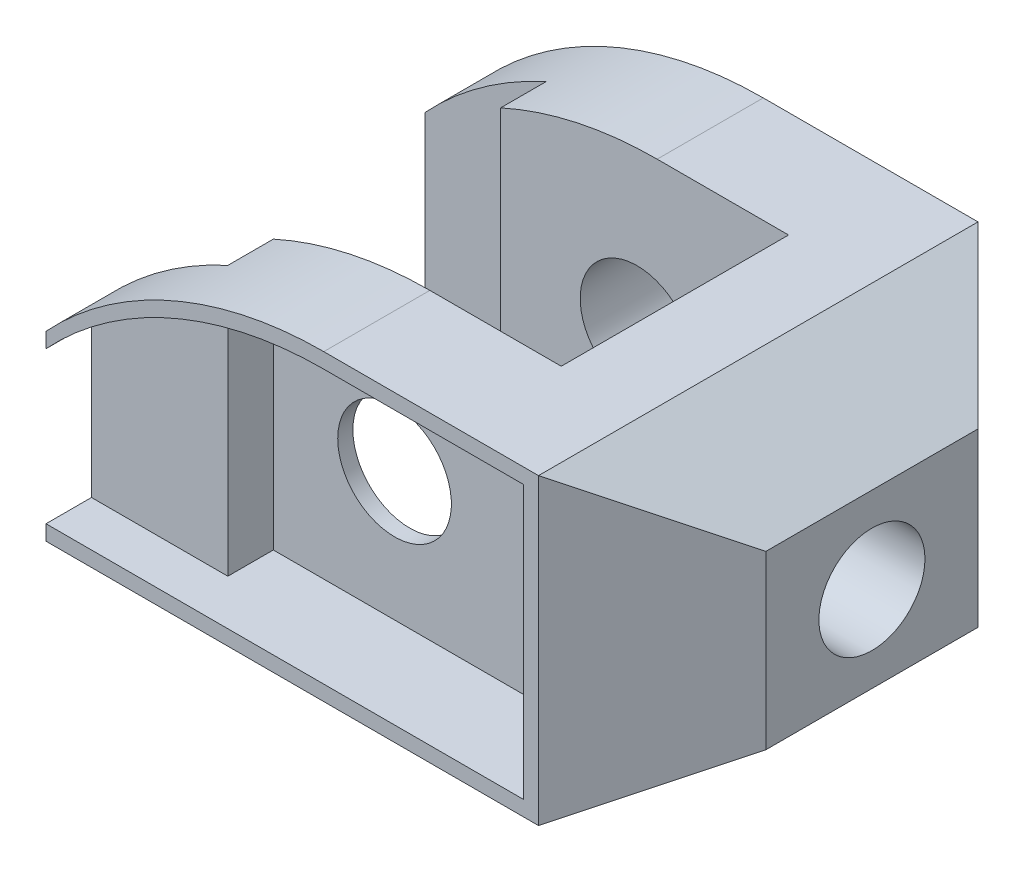
SolidWorks part; units mm, degrees
material "1060 Alloy"
ref_plane "Front Plane" through (0, 0, 0) normal (0, 0, 1) x (1, 0, 0)
ref_plane "Top Plane" through (0, 0, 0) normal (0, 1, 0) x (1, 0, 0)
ref_plane "Right Plane" through (0, 0, 0) normal (1, 0, 0) x (0, 0, -1)
sketch "Sketch1" plane through (0, 0, 0) normal (0, 0, 1) x (1, 0, 0)
  line L0 (-34, -19) -> (31, -19)
  line L1 (-34, -19) -> (-34, 5)
  line L2 (31, -19) -> (31, 21) construction
  line L3 (31, 21) -> (2.6606, 21)
  line L4 (31, 21) -> (46, 12.3397)
  line L5 (31, -19) -> (46, -10.3397)
  line L6 (46, 12.3397) -> (46, -10.3397)
  circle A0 centre (0, 0) radius 7.5
  arc A1 (-34, 5) -> (2.6606, 21) centre (2.6606, -29) cw
  dimension "D1" = 15
  dimension "D4" = 31
  dimension "D7" = 50
  dimension "D2" = 65
  dimension "D3" = 19
  dimension "D5" = 24
  dimension "D6" = 40
  dimension "D8" = 30
  dimension "D9" = 15
  dimension "D10" = 30
  dimension "D11" = 15
extrude "Boss-Extrude1" add sketch "Sketch1" along normal blind 58
sketch "Sketch5" plane through (46, 0, 0) normal (1, 0, 0) x (0, 0, -1)
  line L0 (-58, 1) -> (0, 1) construction
  line L1 (-58, -10.3397) -> (-58, 12.3397) construction
  line L2 (0, -10.3397) -> (0, 12.3397) construction
  circle A0 centre (-29, 1) radius 7
  dimension "D1" = 14
extrude "Cut-Extrude1" cut sketch "Sketch5" against normal through all
sketch "Sketch6" plane through (0, 0, 0) normal (0, 1, 0) x (1, 0, 0)
  line L0 (-34, -14) -> (20, -14)
  line L1 (-34, -23.2554) -> (-34, 0) construction
  line L2 (20, -14) -> (20, -44)
  line L3 (-34, -44) -> (20, -44)
  line L4 (-34, -58) -> (-34, -34.7446) construction
  dimension "D1" = 14
  dimension "D2" = 14
  dimension "D3" = 11
extrude "Cut-Extrude3" cut sketch "Sketch6" against normal through all and the other way through all contours L0 L2 L3
sketch "Sketch7" plane through (0, 0, 0) normal (0, 1, 0) x (1, 0, 0)
  line L0 (-34, -8) -> (-18, -8)
  line L1 (-34, -14) -> (-34, 0) construction
  line L2 (-18, -8) -> (-18, -14)
  line L3 (-34, -14) -> (2.6606, -14) construction
  line L4 (-34, -50) -> (-18, -50)
  line L5 (-34, -58) -> (-34, -44) construction
  line L6 (-18, -50) -> (-18, -44)
  line L7 (2.6606, -44) -> (-34, -44) construction
  line L8 (-18, -44) -> (-34, -44)
  line L9 (-34, -44) -> (-34, -50)
  line L10 (-34, -8) -> (-34, -14)
  line L11 (-34, -14) -> (-18, -14)
  dimension "D1" = 8
  dimension "D2" = 16
  dimension "D3" = 8
  dimension "D4" = 16
extrude "Cut-Extrude5" cut sketch "Sketch7" against normal through all and the other way through all
sketch "Sketch14" plane through (0, 0, 0) normal (0, 1, 0) x (1, 0, 0)
  line L0 (31, 0) -> (46, 0)
  line L1 (46, 0) -> (46, -15)
  line L2 (46, -58) -> (46, 0) construction
  line L3 (46, -15) -> (31, 0)
  line L4 (31, -58) -> (46, -58)
  line L5 (46, -58) -> (46, -43)
  line L6 (46, -43) -> (31, -58)
  dimension "D1" = 45
  dimension "D2" = 45
extrude "Cut-Extrude14" cut sketch "Sketch14" against normal blind 24 and the other way blind 24
sketch "Sketch15" plane through (0, 0, 58) normal (0, 0, 1) x (1, 0, 0)
  line L0 (29, 19) -> (29, -17)
  line L1 (29, -17) -> (-34, -17)
  line L2 (-34, 5) -> (-34, -19) construction
  line L3 (31, 21) -> (31, -19) construction
  line L4 (-34, -19) -> (31, -19) construction
  line L5 (29, 19) -> (2.6606, 19)
  line L6 (31, 21) -> (2.6606, 21) construction
  arc A0 (2.6606, 19) -> (-34, 3) centre (2.6606, -31) ccw
  arc A1 (2.6606, 21) -> (-34, 5) centre (2.6606, -29) ccw construction
  dimension "D4" = 50
  dimension "D5" = 2
  dimension "D1" = 2
  dimension "D2" = 2
  dimension "D3" = 2
extrude "Cut-Extrude16" cut sketch "Sketch15" against normal blind 6 and the other way through all
sketch "Sketch18" plane through (0, 0, 0) normal (0, 1, 0) x (1, 0, 0)
  line L0 (-18, -14) -> (-18, -44) construction
sketch "Sketch19" plane through (0, 0, 52) normal (0, 0, 1) x (1, 0, 0)
  line L0 (29, -17) -> (-16, -17)
  line L1 (29, -17) -> (-34, -17) construction
  line L2 (-16, -17) -> (-16, 15.3873)
  line L3 (29, -17) -> (29, 19)
  line L4 (2.6606, 19) -> (29, 19) construction
  line L5 (2.6606, 19) -> (29, 19)
  line L6 (-34, 3) -> (-34, -17) construction
  arc A0 (-16, 15.3873) -> (2.6606, 19) centre (2.6606, -31) cw
  arc A1 (2.6606, 19) -> (-34, 3) centre (2.6606, -31) ccw construction
  dimension "D2" = 50
  dimension "D1" = 18
extrude "Cut-Extrude19" cut sketch "Sketch19" against normal blind 6 contours L2 A0 L5 L3 L0
equation "\"A\"= 58mm"
equation "\"B\"= 40mm"
equation "\"C\"= 65mm"
